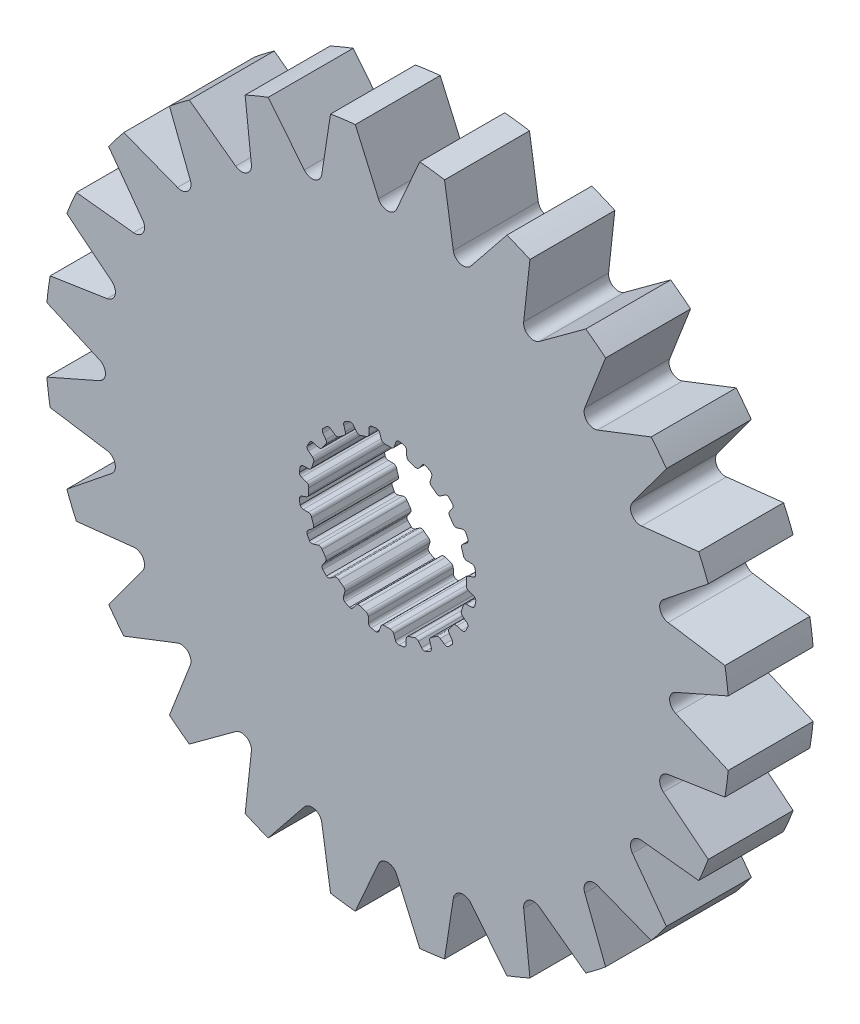
SolidWorks part; units mm, degrees
ref_plane "Front Plane" through (0, 0, 0) normal (0, 0, 1) x (1, 0, 0)
ref_plane "Top Plane" through (0, 0, 0) normal (0, 1, 0) x (1, 0, 0)
ref_plane "Right Plane" through (0, 0, 0) normal (1, 0, 0) x (0, 0, -1)
sketch "Sketch1" plane through (0, 0, 0) normal (0, 0, 1) x (1, 0, 0)
  line L0 (-0.1069, 2.9699) -> (0.1069, 2.9699)
  line L1 (0.3159, 3.2375) -> (0.2537, 3.0575)
  line L2 (-0.2964, 3.2367) -> (-0.2318, 3.0575)
  line L3 (-0.2964, 3.2367) -> (0.3159, 3.2375) construction
  line L4 (0, 3.3252) -> (0, 0) construction
  line L5 (-0.2318, 3.0575) -> (0.2537, 3.0575) construction
  line L6 (-0.4281, 3.3241) -> (0.4281, 3.3263) construction
  line L7 (0.7183, 3.1698) -> (0.7244, 2.9795)
  line L8 (0.816, 2.8576) -> (1.0195, 2.7915)
  line L9 (1.3009, 2.9815) -> (1.1862, 2.8295)
  line L10 (1.6627, 2.7927) -> (1.6097, 2.6099)
  line L11 (1.6591, 2.4655) -> (1.8322, 2.3398)
  line L12 (2.1585, 2.4335) -> (2.0025, 2.3245)
  line L13 (2.4443, 2.1423) -> (2.3374, 1.9847)
  line L14 (2.3398, 1.8322) -> (2.4655, 1.6591)
  line L15 (2.8049, 1.6474) -> (2.6228, 1.5919)
  line L16 (2.9866, 1.2821) -> (2.8363, 1.1653)
  line L17 (2.7915, 1.0195) -> (2.8576, 0.816)
  line L18 (3.1767, 0.7) -> (2.9863, 0.7035)
  line L19 (3.2367, 0.2964) -> (3.0575, 0.2318)
  line L20 (2.9699, 0.1069) -> (2.9699, -0.1069)
  line L21 (3.2375, -0.3159) -> (3.0575, -0.2537)
  line L22 (3.1698, -0.7183) -> (2.9795, -0.7244)
  line L23 (2.8576, -0.816) -> (2.7915, -1.0195)
  line L24 (2.9815, -1.3009) -> (2.8295, -1.1862)
  line L25 (2.7927, -1.6627) -> (2.6099, -1.6097)
  line L26 (2.4655, -1.6591) -> (2.3398, -1.8322)
  line L27 (2.4335, -2.1585) -> (2.3245, -2.0025)
  line L28 (2.1423, -2.4443) -> (1.9847, -2.3374)
  line L29 (1.8322, -2.3398) -> (1.6591, -2.4655)
  line L30 (1.6474, -2.8049) -> (1.5919, -2.6228)
  line L31 (1.2821, -2.9866) -> (1.1653, -2.8363)
  line L32 (1.0195, -2.7915) -> (0.816, -2.8576)
  line L33 (0.7, -3.1767) -> (0.7035, -2.9863)
  line L34 (0.2964, -3.2367) -> (0.2318, -3.0575)
  line L35 (0.1069, -2.9699) -> (-0.1069, -2.9699)
  line L36 (-0.3159, -3.2375) -> (-0.2537, -3.0575)
  line L37 (-0.7183, -3.1698) -> (-0.7244, -2.9795)
  line L38 (-0.816, -2.8576) -> (-1.0195, -2.7915)
  line L39 (-1.3009, -2.9815) -> (-1.1862, -2.8295)
  line L40 (-1.6627, -2.7927) -> (-1.6097, -2.6099)
  line L41 (-1.6591, -2.4655) -> (-1.8322, -2.3398)
  line L42 (-2.1585, -2.4335) -> (-2.0025, -2.3245)
  line L43 (-2.4443, -2.1423) -> (-2.3374, -1.9847)
  line L44 (-2.3398, -1.8322) -> (-2.4655, -1.6591)
  line L45 (-2.8049, -1.6474) -> (-2.6228, -1.5919)
  line L46 (-2.9866, -1.2821) -> (-2.8363, -1.1653)
  line L47 (-2.7915, -1.0195) -> (-2.8576, -0.816)
  line L48 (-3.1767, -0.7) -> (-2.9863, -0.7035)
  line L49 (-3.2367, -0.2964) -> (-3.0575, -0.2318)
  line L50 (-2.9699, -0.1069) -> (-2.9699, 0.1069)
  line L51 (-3.2375, 0.3159) -> (-3.0575, 0.2537)
  line L52 (-3.1698, 0.7183) -> (-2.9795, 0.7244)
  line L53 (-2.8576, 0.816) -> (-2.7915, 1.0195)
  line L54 (-2.9815, 1.3009) -> (-2.8295, 1.1862)
  line L55 (-2.7927, 1.6627) -> (-2.6099, 1.6097)
  line L56 (-2.4655, 1.6591) -> (-2.3398, 1.8322)
  line L57 (-2.4335, 2.1585) -> (-2.3245, 2.0025)
  line L58 (-2.1423, 2.4443) -> (-1.9847, 2.3374)
  line L59 (-1.8322, 2.3398) -> (-1.6591, 2.4655)
  line L60 (-1.6474, 2.8049) -> (-1.5919, 2.6228)
  line L61 (-1.2821, 2.9866) -> (-1.1653, 2.8363)
  line L62 (-1.0195, 2.7915) -> (-0.816, 2.8576)
  line L63 (-0.7, 3.1767) -> (-0.7035, 2.9863)
  line L64 (0.4281, 3.3263) -> (0.62, 3.2938)
  line L65 (1.4351, 3.0312) -> (1.6075, 2.9409)
  line L66 (2.3015, 2.4394) -> (2.4376, 2.3003)
  line L67 (2.9427, 1.6088) -> (3.0291, 1.4344)
  line L68 (3.2958, 0.6207) -> (3.3241, 0.4281)
  line L69 (3.3263, -0.4281) -> (3.2938, -0.62)
  line L70 (3.0312, -1.4351) -> (2.9409, -1.6075)
  line L71 (2.4394, -2.3015) -> (2.3003, -2.4376)
  line L72 (1.6088, -2.9427) -> (1.4344, -3.0291)
  line L73 (0.6207, -3.2958) -> (0.4281, -3.3241)
  line L74 (-0.4281, -3.3263) -> (-0.62, -3.2938)
  line L75 (-1.4351, -3.0312) -> (-1.6075, -2.9409)
  line L76 (-2.3015, -2.4394) -> (-2.4376, -2.3003)
  line L77 (-2.9427, -1.6088) -> (-3.0291, -1.4344)
  line L78 (-3.2958, -0.6207) -> (-3.3241, -0.4281)
  line L79 (-3.3263, 0.4281) -> (-3.2938, 0.62)
  line L80 (-3.0312, 1.4351) -> (-2.9409, 1.6075)
  line L81 (-2.4394, 2.3015) -> (-2.3003, 2.4376)
  line L82 (-1.6088, 2.9427) -> (-1.4344, 3.0291)
  line L83 (-0.6207, 3.2958) -> (-0.4281, 3.3241)
  arc A0 (0.2537, 3.0575) -> (0.1069, 2.9699) centre (0.1283, 3.1009) cw
  arc A1 (-0.2318, 3.0575) -> (-0.1069, 2.9699) centre (-0.1069, 3.1026) ccw
  arc A2 (0.62, 3.2938) -> (0.7183, 3.1698) centre (0.5856, 3.1656) cw
  arc A3 (0.7244, 2.9795) -> (0.816, 2.8576) centre (0.857, 2.9838) ccw
  arc A4 (-0.4281, 3.3241) -> (-0.2964, 3.2367) centre (-0.4213, 3.1916) cw
  arc A5 (0.4281, 3.3263) -> (0.3159, 3.2375) centre (0.4413, 3.1942) ccw
  arc A6 (1.1862, 2.8295) -> (1.0195, 2.7915) centre (1.0802, 2.9095) cw
  arc A7 (1.4351, 3.0312) -> (1.3009, 2.9815) centre (1.4068, 2.9015) ccw
  arc A8 (1.6075, 2.9409) -> (1.6627, 2.7927) centre (1.5352, 2.8297) cw
  arc A9 (1.6097, 2.6099) -> (1.6591, 2.4655) centre (1.7371, 2.5729) ccw
  arc A10 (2.0025, 2.3245) -> (1.8322, 2.3398) centre (1.9264, 2.4332) cw
  arc A11 (2.3015, 2.4394) -> (2.1585, 2.4335) centre (2.2346, 2.3248) ccw
  arc A12 (2.4376, 2.3003) -> (2.4443, 2.1423) centre (2.3345, 2.2168) cw
  arc A13 (2.3374, 1.9847) -> (2.3398, 1.8322) centre (2.4472, 1.9102) ccw
  arc A14 (2.6228, 1.5919) -> (2.4655, 1.6591) centre (2.5841, 1.7189) cw
  arc A15 (2.9427, 1.6088) -> (2.8049, 1.6474) centre (2.8436, 1.5205) ccw
  arc A16 (3.0291, 1.4344) -> (2.9866, 1.2821) centre (2.9052, 1.3869) cw
  arc A17 (2.8363, 1.1653) -> (2.7915, 1.0195) centre (2.9177, 1.0605) ccw
  arc A18 (2.9863, 0.7035) -> (2.8576, 0.816) centre (2.9887, 0.8362) cw
  arc A19 (3.2958, 0.6207) -> (3.1767, 0.7) centre (3.1743, 0.5673) ccw
  arc A20 (3.3241, 0.4281) -> (3.2367, 0.2964) centre (3.1916, 0.4213) cw
  arc A21 (3.0575, 0.2318) -> (2.9699, 0.1069) centre (3.1026, 0.1069) ccw
  arc A22 (3.0575, -0.2537) -> (2.9699, -0.1069) centre (3.1009, -0.1283) cw
  arc A23 (3.3263, -0.4281) -> (3.2375, -0.3159) centre (3.1942, -0.4413) ccw
  arc A24 (3.2938, -0.62) -> (3.1698, -0.7183) centre (3.1656, -0.5856) cw
  arc A25 (2.9795, -0.7244) -> (2.8576, -0.816) centre (2.9838, -0.857) ccw
  arc A26 (2.8295, -1.1862) -> (2.7915, -1.0195) centre (2.9095, -1.0802) cw
  arc A27 (3.0312, -1.4351) -> (2.9815, -1.3009) centre (2.9015, -1.4068) ccw
  arc A28 (2.9409, -1.6075) -> (2.7927, -1.6627) centre (2.8297, -1.5352) cw
  arc A29 (2.6099, -1.6097) -> (2.4655, -1.6591) centre (2.5729, -1.7371) ccw
  arc A30 (2.3245, -2.0025) -> (2.3398, -1.8322) centre (2.4332, -1.9264) cw
  arc A31 (2.4394, -2.3015) -> (2.4335, -2.1585) centre (2.3248, -2.2346) ccw
  arc A32 (2.3003, -2.4376) -> (2.1423, -2.4443) centre (2.2168, -2.3345) cw
  arc A33 (1.9847, -2.3374) -> (1.8322, -2.3398) centre (1.9102, -2.4472) ccw
  arc A34 (1.5919, -2.6228) -> (1.6591, -2.4655) centre (1.7189, -2.5841) cw
  arc A35 (1.6088, -2.9427) -> (1.6474, -2.8049) centre (1.5205, -2.8436) ccw
  arc A36 (1.4344, -3.0291) -> (1.2821, -2.9866) centre (1.3869, -2.9052) cw
  arc A37 (1.1653, -2.8363) -> (1.0195, -2.7915) centre (1.0605, -2.9177) ccw
  arc A38 (0.7035, -2.9863) -> (0.816, -2.8576) centre (0.8362, -2.9887) cw
  arc A39 (0.6207, -3.2958) -> (0.7, -3.1767) centre (0.5673, -3.1743) ccw
  arc A40 (0.4281, -3.3241) -> (0.2964, -3.2367) centre (0.4213, -3.1916) cw
  arc A41 (0.2318, -3.0575) -> (0.1069, -2.9699) centre (0.1069, -3.1026) ccw
  arc A42 (-0.2537, -3.0575) -> (-0.1069, -2.9699) centre (-0.1283, -3.1009) cw
  arc A43 (-0.4281, -3.3263) -> (-0.3159, -3.2375) centre (-0.4413, -3.1942) ccw
  arc A44 (-0.62, -3.2938) -> (-0.7183, -3.1698) centre (-0.5856, -3.1656) cw
  arc A45 (-0.7244, -2.9795) -> (-0.816, -2.8576) centre (-0.857, -2.9838) ccw
  arc A46 (-1.1862, -2.8295) -> (-1.0195, -2.7915) centre (-1.0802, -2.9095) cw
  arc A47 (-1.4351, -3.0312) -> (-1.3009, -2.9815) centre (-1.4068, -2.9015) ccw
  arc A48 (-1.6075, -2.9409) -> (-1.6627, -2.7927) centre (-1.5352, -2.8297) cw
  arc A49 (-1.6097, -2.6099) -> (-1.6591, -2.4655) centre (-1.7371, -2.5729) ccw
  arc A50 (-2.0025, -2.3245) -> (-1.8322, -2.3398) centre (-1.9264, -2.4332) cw
  arc A51 (-2.3015, -2.4394) -> (-2.1585, -2.4335) centre (-2.2346, -2.3248) ccw
  arc A52 (-2.4376, -2.3003) -> (-2.4443, -2.1423) centre (-2.3345, -2.2168) cw
  arc A53 (-2.3374, -1.9847) -> (-2.3398, -1.8322) centre (-2.4472, -1.9102) ccw
  arc A54 (-2.6228, -1.5919) -> (-2.4655, -1.6591) centre (-2.5841, -1.7189) cw
  arc A55 (-2.9427, -1.6088) -> (-2.8049, -1.6474) centre (-2.8436, -1.5205) ccw
  arc A56 (-3.0291, -1.4344) -> (-2.9866, -1.2821) centre (-2.9052, -1.3869) cw
  arc A57 (-2.8363, -1.1653) -> (-2.7915, -1.0195) centre (-2.9177, -1.0605) ccw
  arc A58 (-2.9863, -0.7035) -> (-2.8576, -0.816) centre (-2.9887, -0.8362) cw
  arc A59 (-3.2958, -0.6207) -> (-3.1767, -0.7) centre (-3.1743, -0.5673) ccw
  arc A60 (-3.3241, -0.4281) -> (-3.2367, -0.2964) centre (-3.1916, -0.4213) cw
  arc A61 (-3.0575, -0.2318) -> (-2.9699, -0.1069) centre (-3.1026, -0.1069) ccw
  arc A62 (-3.0575, 0.2537) -> (-2.9699, 0.1069) centre (-3.1009, 0.1283) cw
  arc A63 (-3.3263, 0.4281) -> (-3.2375, 0.3159) centre (-3.1942, 0.4413) ccw
  arc A64 (-3.2938, 0.62) -> (-3.1698, 0.7183) centre (-3.1656, 0.5856) cw
  arc A65 (-2.9795, 0.7244) -> (-2.8576, 0.816) centre (-2.9838, 0.857) ccw
  arc A66 (-2.8295, 1.1862) -> (-2.7915, 1.0195) centre (-2.9095, 1.0802) cw
  arc A67 (-3.0312, 1.4351) -> (-2.9815, 1.3009) centre (-2.9015, 1.4068) ccw
  arc A68 (-2.9409, 1.6075) -> (-2.7927, 1.6627) centre (-2.8297, 1.5352) cw
  arc A69 (-2.6099, 1.6097) -> (-2.4655, 1.6591) centre (-2.5729, 1.7371) ccw
  arc A70 (-2.3245, 2.0025) -> (-2.3398, 1.8322) centre (-2.4332, 1.9264) cw
  arc A71 (-2.4394, 2.3015) -> (-2.4335, 2.1585) centre (-2.3248, 2.2346) ccw
  arc A72 (-2.3003, 2.4376) -> (-2.1423, 2.4443) centre (-2.2168, 2.3345) cw
  arc A73 (-1.9847, 2.3374) -> (-1.8322, 2.3398) centre (-1.9102, 2.4472) ccw
  arc A74 (-1.5919, 2.6228) -> (-1.6591, 2.4655) centre (-1.7189, 2.5841) cw
  arc A75 (-1.6088, 2.9427) -> (-1.6474, 2.8049) centre (-1.5205, 2.8436) ccw
  arc A76 (-1.4344, 3.0291) -> (-1.2821, 2.9866) centre (-1.3869, 2.9052) cw
  arc A77 (-1.1653, 2.8363) -> (-1.0195, 2.7915) centre (-1.0605, 2.9177) ccw
  arc A78 (-0.7035, 2.9863) -> (-0.816, 2.8576) centre (-0.8362, 2.9887) cw
  arc A79 (-0.6207, 3.2958) -> (-0.7, 3.1767) centre (-0.5673, 3.1743) ccw
  circle A80 centre (0, 0) radius 12.8934
  point P14 (0, 2.9699)
  point P247 (0, 0)
  dimension "D4" = 0.1327
  dimension "D8" = 20
  dimension "D9" = 25.7868
  dimension "D1" = 2.9699
  dimension "D2" = 0.2139
  dimension "D3" = 0.1904
  dimension "D5" = 0.0877
  dimension "D6" = 0.4855
  dimension "D7" = 0.8563
extrude "Boss-Extrude1" add sketch "Sketch1" along normal mid plane 3.2004
sketch "Sketch2" plane through (0, 0, 1.6002) normal (0, 0, 1) x (1, 0, 0)
  line L0 (0, 12.836) -> (0, 0) construction
  line L1 (1.557, 23.6884) -> (0, 0) construction
  line L2 (-1.2151, 12.836) -> (1.2151, 12.836) construction
  line L3 (-0.7785, 11.8442) -> (0.7785, 11.8442) construction
  line L4 (-1.2151, 12.836) -> (-0.3419, 10.8524)
  line L5 (1.2151, 12.836) -> (0.3419, 10.8524)
  line L6 (4.4959, 12.0841) -> (3.1391, 10.3941)
  line L7 (2.1485, 12.7131) -> (2.4786, 10.5711)
  line L8 (7.4703, 10.5087) -> (5.7223, 9.2275)
  line L9 (5.3657, 11.7239) -> (5.1301, 9.5694)
  line L10 (9.9357, 8.2172) -> (7.9156, 7.4321)
  line L11 (8.2172, 9.9357) -> (7.4321, 7.9156)
  line L12 (11.7239, 5.3657) -> (9.5694, 5.1301)
  line L13 (10.5087, 7.4703) -> (9.2275, 5.7223)
  line L14 (12.7131, 2.1485) -> (10.5711, 2.4786)
  line L15 (12.0841, 4.4959) -> (10.3941, 3.1391)
  line L16 (12.836, -1.2151) -> (10.8524, -0.3419)
  line L17 (12.836, 1.2151) -> (10.8524, 0.3419)
  line L18 (12.0841, -4.4959) -> (10.3941, -3.1391)
  line L19 (12.7131, -2.1485) -> (10.5711, -2.4786)
  line L20 (10.5087, -7.4703) -> (9.2275, -5.7223)
  line L21 (11.7239, -5.3657) -> (9.5694, -5.1301)
  line L22 (8.2172, -9.9357) -> (7.4321, -7.9156)
  line L23 (9.9357, -8.2172) -> (7.9156, -7.4321)
  line L24 (5.3657, -11.7239) -> (5.1301, -9.5694)
  line L25 (7.4703, -10.5087) -> (5.7223, -9.2275)
  line L26 (2.1485, -12.7131) -> (2.4786, -10.5711)
  line L27 (4.4959, -12.0841) -> (3.1391, -10.3941)
  line L28 (-1.2151, -12.836) -> (-0.3419, -10.8524)
  line L29 (1.2151, -12.836) -> (0.3419, -10.8524)
  line L30 (-4.4959, -12.0841) -> (-3.1391, -10.3941)
  line L31 (-2.1485, -12.7131) -> (-2.4786, -10.5711)
  line L32 (-7.4703, -10.5087) -> (-5.7223, -9.2275)
  line L33 (-5.3657, -11.7239) -> (-5.1301, -9.5694)
  line L34 (-9.9357, -8.2172) -> (-7.9156, -7.4321)
  line L35 (-8.2172, -9.9357) -> (-7.4321, -7.9156)
  line L36 (-11.7239, -5.3657) -> (-9.5694, -5.1301)
  line L37 (-10.5087, -7.4703) -> (-9.2275, -5.7223)
  line L38 (-12.7131, -2.1485) -> (-10.5711, -2.4786)
  line L39 (-12.0841, -4.4959) -> (-10.3941, -3.1391)
  line L40 (-12.836, 1.2151) -> (-10.8524, 0.3419)
  line L41 (-12.836, -1.2151) -> (-10.8524, -0.3419)
  line L42 (-12.0841, 4.4959) -> (-10.3941, 3.1391)
  line L43 (-12.7131, 2.1485) -> (-10.5711, 2.4786)
  line L44 (-10.5087, 7.4703) -> (-9.2275, 5.7223)
  line L45 (-11.7239, 5.3657) -> (-9.5694, 5.1301)
  line L46 (-8.2172, 9.9357) -> (-7.4321, 7.9156)
  line L47 (-9.9357, 8.2172) -> (-7.9156, 7.4321)
  line L48 (-5.3657, 11.7239) -> (-5.1301, 9.5694)
  line L49 (-7.4703, 10.5087) -> (-5.7223, 9.2275)
  line L50 (-2.1485, 12.7131) -> (-2.4786, 10.5711)
  line L51 (-4.4959, 12.0841) -> (-3.1391, 10.3941)
  circle A0 centre (0, 0) radius 12.8934 construction
  arc A1 (-0.3419, 10.8524) -> (0.3419, 10.8524) centre (0, 11.0029) ccw
  arc A2 (-1.2151, 12.836) -> (1.2151, 12.836) centre (0, 0) cw
  arc A3 (2.1485, 12.7131) -> (4.4959, 12.0841) centre (0, 0) cw
  arc A4 (2.4786, 10.5711) -> (3.1391, 10.3941) centre (2.8478, 10.628) ccw
  arc A5 (5.3657, 11.7239) -> (7.4703, 10.5087) centre (0, 0) cw
  arc A6 (5.1301, 9.5694) -> (5.7223, 9.2275) centre (5.5015, 9.5288) ccw
  arc A7 (8.2172, 9.9357) -> (9.9357, 8.2172) centre (0, 0) cw
  arc A8 (7.4321, 7.9156) -> (7.9156, 7.4321) centre (7.7802, 7.7802) ccw
  arc A9 (10.5087, 7.4703) -> (11.7239, 5.3657) centre (0, 0) cw
  arc A10 (9.2275, 5.7223) -> (9.5694, 5.1301) centre (9.5288, 5.5015) ccw
  arc A11 (12.0841, 4.4959) -> (12.7131, 2.1485) centre (0, 0) cw
  arc A12 (10.3941, 3.1391) -> (10.5711, 2.4786) centre (10.628, 2.8478) ccw
  arc A13 (12.836, 1.2151) -> (12.836, -1.2151) centre (0, 0) cw
  arc A14 (10.8524, 0.3419) -> (10.8524, -0.3419) centre (11.0029, 0) ccw
  arc A15 (12.7131, -2.1485) -> (12.0841, -4.4959) centre (0, 0) cw
  arc A16 (10.5711, -2.4786) -> (10.3941, -3.1391) centre (10.628, -2.8478) ccw
  arc A17 (11.7239, -5.3657) -> (10.5087, -7.4703) centre (0, 0) cw
  arc A18 (9.5694, -5.1301) -> (9.2275, -5.7223) centre (9.5288, -5.5015) ccw
  arc A19 (9.9357, -8.2172) -> (8.2172, -9.9357) centre (0, 0) cw
  arc A20 (7.9156, -7.4321) -> (7.4321, -7.9156) centre (7.7802, -7.7802) ccw
  arc A21 (7.4703, -10.5087) -> (5.3657, -11.7239) centre (0, 0) cw
  arc A22 (5.7223, -9.2275) -> (5.1301, -9.5694) centre (5.5015, -9.5288) ccw
  arc A23 (4.4959, -12.0841) -> (2.1485, -12.7131) centre (0, 0) cw
  arc A24 (3.1391, -10.3941) -> (2.4786, -10.5711) centre (2.8478, -10.628) ccw
  arc A25 (1.2151, -12.836) -> (-1.2151, -12.836) centre (0, 0) cw
  arc A26 (0.3419, -10.8524) -> (-0.3419, -10.8524) centre (0, -11.0029) ccw
  arc A27 (-2.1485, -12.7131) -> (-4.4959, -12.0841) centre (0, 0) cw
  arc A28 (-2.4786, -10.5711) -> (-3.1391, -10.3941) centre (-2.8478, -10.628) ccw
  arc A29 (-5.3657, -11.7239) -> (-7.4703, -10.5087) centre (0, 0) cw
  arc A30 (-5.1301, -9.5694) -> (-5.7223, -9.2275) centre (-5.5015, -9.5288) ccw
  arc A31 (-8.2172, -9.9357) -> (-9.9357, -8.2172) centre (0, 0) cw
  arc A32 (-7.4321, -7.9156) -> (-7.9156, -7.4321) centre (-7.7802, -7.7802) ccw
  arc A33 (-10.5087, -7.4703) -> (-11.7239, -5.3657) centre (0, 0) cw
  arc A34 (-9.2275, -5.7223) -> (-9.5694, -5.1301) centre (-9.5288, -5.5015) ccw
  arc A35 (-12.0841, -4.4959) -> (-12.7131, -2.1485) centre (0, 0) cw
  arc A36 (-10.3941, -3.1391) -> (-10.5711, -2.4786) centre (-10.628, -2.8478) ccw
  arc A37 (-12.836, -1.2151) -> (-12.836, 1.2151) centre (0, 0) cw
  arc A38 (-10.8524, -0.3419) -> (-10.8524, 0.3419) centre (-11.0029, 0) ccw
  arc A39 (-12.7131, 2.1485) -> (-12.0841, 4.4959) centre (0, 0) cw
  arc A40 (-10.5711, 2.4786) -> (-10.3941, 3.1391) centre (-10.628, 2.8478) ccw
  arc A41 (-11.7239, 5.3657) -> (-10.5087, 7.4703) centre (0, 0) cw
  arc A42 (-9.5694, 5.1301) -> (-9.2275, 5.7223) centre (-9.5288, 5.5015) ccw
  arc A43 (-9.9357, 8.2172) -> (-8.2172, 9.9357) centre (0, 0) cw
  arc A44 (-7.9156, 7.4321) -> (-7.4321, 7.9156) centre (-7.7802, 7.7802) ccw
  arc A45 (-7.4703, 10.5087) -> (-5.3657, 11.7239) centre (0, 0) cw
  arc A46 (-5.7223, 9.2275) -> (-5.1301, 9.5694) centre (-5.5015, 9.5288) ccw
  arc A47 (-4.4959, 12.0841) -> (-2.1485, 12.7131) centre (0, 0) cw
  arc A48 (-3.1391, 10.3941) -> (-2.4786, 10.5711) centre (-2.8478, 10.628) ccw
  point P9 (0, 11.8442)
  point P132 (0, 0)
  dimension "D1" = 0.9918
  dimension "D2" = 1.557
  dimension "D3" = 20
  dimension "D4" = 24
extrude "Cut-Extrude1" cut sketch "Sketch2" against normal up to surface (3.2004 mm away) up to face at (12.8934, 0, -1.6002)
sketch "Sketch3" plane through (0, 0, 1.6002) normal (0, 0, 1) x (1, 0, 0)
  circle A0 centre (0, 0) radius 11.9016 construction
  circle A1 centre (0, 0) radius 12.8934 construction
  dimension "D1" = 23.8032
